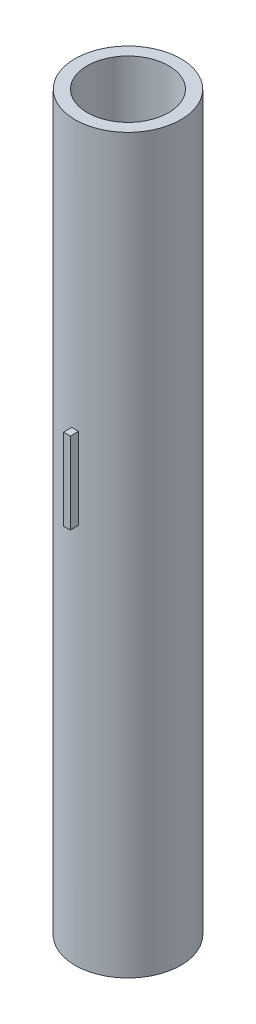
SolidWorks part; units mm, degrees
ref_plane "Front Plane" through (0, 0, 0) normal (0, 0, 1) x (1, 0, 0)
ref_plane "Top Plane" through (0, 0, 0) normal (0, 1, 0) x (1, 0, 0)
ref_plane "Right Plane" through (0, 0, 0) normal (1, 0, 0) x (0, 0, -1)
sketch "Sketch1" plane through (0, 0, 0) normal (0, 1, 0) x (1, 0, 0)
  circle A0 centre (0, 0) radius 19.5
  circle A1 centre (0, 0) radius 15
extrude "Boss-Extrude1" add sketch "Sketch1" along normal blind 270
ref_plane "Plane1" through (0, 0, 22.5) normal (0, 0, 1) x (1, 0, 0)
sketch "Sketch3" plane through (0, 0, 22.5) normal (0, 0, 1) x (1, 0, 0)
  line L1 (1.25, 171.1169) -> (-1.25, 171.1169)
  line L2 (1.25, 171.1169) -> (1.25, 141.1169)
  line L3 (1.25, 141.1169) -> (-1.25, 141.1169)
  line L4 (-1.25, 171.1169) -> (-1.25, 141.1169)
  line L5 (1.25, 171.1169) -> (-1.25, 141.1169) construction
  line L6 (1.25, 141.1169) -> (-1.25, 171.1169) construction
  point P0 (0, 156.1169)
extrude "Boss-Extrude2" add sketch "Sketch3" against normal blind 6
